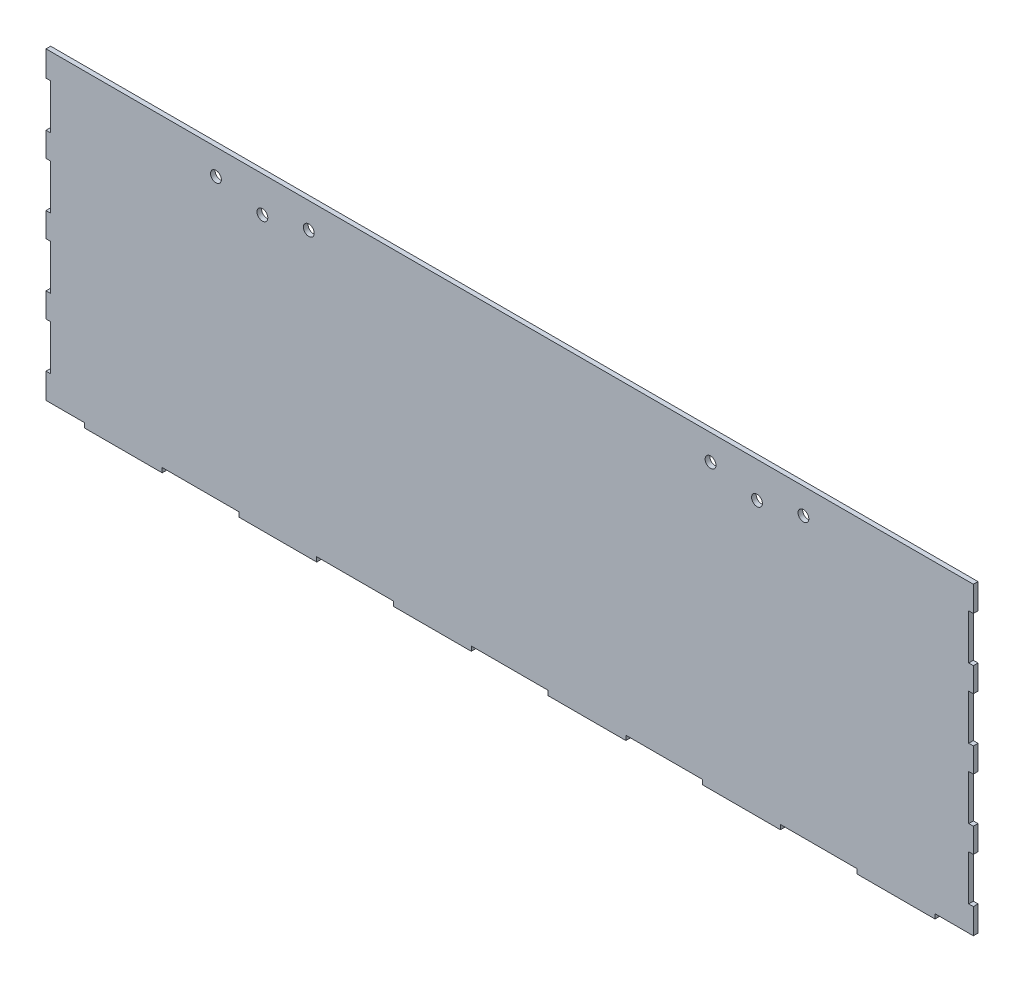
SolidWorks part; units mm, degrees
ref_plane "Alzado" through (0, 0, 0) normal (0, 0, 1) x (1, 0, 0)
ref_plane "Planta" through (0, 0, 0) normal (0, 1, 0) x (1, 0, 0)
ref_plane "Vista lateral" through (0, 0, 0) normal (1, 0, 0) x (0, 0, -1)
sketch "Croquis1" plane through (0, 0, 0) normal (0, 0, 1) x (1, 0, 0)
  line L1 (-300, 100) -> (300, 100)
  line L2 (-300, 100) -> (-300, -100)
  line L3 (-300, -100) -> (300, -100)
  line L4 (300, 100) -> (300, -100)
  line L5 (-300, 100) -> (300, -100) construction
  line L6 (-300, -100) -> (300, 100) construction
  point P0 (0, 0)
  dimension "D1" = 600
  dimension "D2" = 200
extrude "Saliente-Extruir1" add sketch "Croquis1" along normal blind 3
sketch "Croquis2" plane through (0, 0, 0) normal (0, 0, -1) x (-1, 0, 0)
  line L4 (-300, 100) -> (-300, -100)
  line L5 (-300, -100) -> (300, -100)
  line L6 (300, -100) -> (300, 100)
  line L7 (300, 100) -> (-300, 100)
  line L9 (-300, -100) -> (300, -100)
  line L11 (300, 100) -> (-300, 100)
  line L68 (224.85, -100) -> (275.15, -100)
  line L69 (275.15, -100) -> (275.15, -97)
  line L70 (275.15, -97) -> (300, -97)
  line L71 (300, -97) -> (300, -81)
  line L72 (300, -81) -> (297, -81)
  line L73 (297, -81) -> (297, -51)
  line L74 (297, -51) -> (300, -51)
  line L75 (300, -51) -> (300, -36)
  line L76 (300, -36) -> (297, -36)
  line L77 (297, -36) -> (297, -6)
  line L78 (297, -6) -> (300, -6)
  line L79 (300, -6) -> (300, 9)
  line L80 (300, 9) -> (297, 9)
  line L81 (297, 9) -> (297, 39)
  line L82 (297, 39) -> (300, 39)
  line L83 (300, 39) -> (300, 54)
  line L84 (300, 54) -> (297, 54)
  line L85 (297, 54) -> (297, 84)
  line L86 (297, 84) -> (300, 84)
  line L87 (300, 84) -> (300, 100)
  line L88 (300, 100) -> (-300, 100)
  line L89 (-300, 100) -> (-300, 84)
  line L90 (-300, 84) -> (-297, 84)
  line L91 (-297, 84) -> (-297, 54)
  line L92 (-297, 54) -> (-300, 54)
  line L93 (-300, 54) -> (-300, 39)
  line L94 (-300, 39) -> (-297, 39)
  line L95 (-297, 39) -> (-297, 9)
  line L96 (-297, 9) -> (-300, 9)
  line L97 (-300, 9) -> (-300, -6)
  line L98 (-300, -6) -> (-297, -6)
  line L99 (-297, -6) -> (-297, -36)
  line L100 (-297, -36) -> (-300, -36)
  line L101 (-300, -36) -> (-300, -51)
  line L102 (-300, -51) -> (-297, -51)
  line L103 (-297, -51) -> (-297, -81)
  line L104 (-297, -81) -> (-300, -81)
  line L105 (-300, -81) -> (-300, -97)
  line L106 (-300, -97) -> (-275.15, -97)
  line L107 (-275.15, -97) -> (-275.15, -100)
  line L108 (-275.15, -100) -> (-224.85, -100)
  line L109 (-224.85, -100) -> (-224.85, -97)
  line L110 (-224.85, -97) -> (-175.15, -97)
  line L111 (-175.15, -97) -> (-175.15, -100)
  line L112 (-175.15, -100) -> (-124.85, -100)
  line L113 (-124.85, -100) -> (-124.85, -97)
  line L114 (-124.85, -97) -> (-75.15, -97)
  line L115 (-75.15, -97) -> (-75.15, -100)
  line L116 (-75.15, -100) -> (-24.85, -100)
  line L117 (-24.85, -100) -> (-24.85, -97)
  line L118 (-24.85, -97) -> (24.85, -97)
  line L119 (24.85, -97) -> (24.85, -100)
  line L120 (24.85, -100) -> (75.15, -100)
  line L121 (75.15, -100) -> (75.15, -97)
  line L122 (75.15, -97) -> (124.85, -97)
  line L123 (124.85, -97) -> (124.85, -100)
  line L124 (124.85, -100) -> (175.15, -100)
  line L125 (175.15, -100) -> (175.15, -97)
  line L126 (175.15, -97) -> (224.85, -97)
  line L127 (224.85, -97) -> (224.85, -100)
  line L128 (224.85, -100) -> (275.15, -100)
  line L129 (275.15, -100) -> (275.15, -97)
  line L130 (275.15, -97) -> (300, -97)
  line L148 (300, 100) -> (-300, 100)
  line L166 (-300, -97) -> (-275.15, -97)
  line L167 (-275.15, -97) -> (-275.15, -100)
  line L168 (-275.15, -100) -> (-224.85, -100)
  line L169 (-224.85, -100) -> (-224.85, -97)
  line L170 (-224.85, -97) -> (-175.15, -97)
  line L171 (-175.15, -97) -> (-175.15, -100)
  line L172 (-175.15, -100) -> (-124.85, -100)
  line L173 (-124.85, -100) -> (-124.85, -97)
  line L174 (-124.85, -97) -> (-75.15, -97)
  line L175 (-75.15, -97) -> (-75.15, -100)
  line L176 (-75.15, -100) -> (-24.85, -100)
  line L177 (-24.85, -100) -> (-24.85, -97)
  line L178 (-24.85, -97) -> (24.85, -97)
  line L179 (24.85, -97) -> (24.85, -100)
  line L180 (24.85, -100) -> (75.15, -100)
  line L181 (75.15, -100) -> (75.15, -97)
  line L182 (75.15, -97) -> (124.85, -97)
  line L183 (124.85, -97) -> (124.85, -100)
  line L184 (124.85, -100) -> (175.15, -100)
  line L185 (175.15, -100) -> (175.15, -97)
  line L186 (175.15, -97) -> (224.85, -97)
  line L187 (224.85, -97) -> (224.85, -100)
  line L548 (-300, -97) -> (-300, 100)
  line L549 (300, -100) -> (300, 100)
  line L731 (-297, -51.4) -> (-300, -51.4)
  line L732 (-297, -51.4) -> (-297, -80.6)
  line L733 (-297, -80.6) -> (-300, -80.6)
  line L734 (-300, -51.4) -> (-300, -80.6)
  line L1814 (-297, -6.4) -> (-297, -35.6)
  line L1815 (-297, -6.4) -> (-300, -6.4)
  line L1816 (-300, -6.4) -> (-300, -35.6)
  line L1817 (-297, -35.6) -> (-300, -35.6)
  line L1818 (-297, 38.6) -> (-297, 9.4)
  line L1819 (-297, 38.6) -> (-300, 38.6)
  line L1820 (-300, 38.6) -> (-300, 9.4)
  line L1821 (-297, 9.4) -> (-300, 9.4)
  line L1822 (-297, 83.6) -> (-297, 54.4)
  line L1823 (-297, 83.6) -> (-300, 83.6)
  line L1824 (-300, 83.6) -> (-300, 54.4)
  line L1825 (-297, 54.4) -> (-300, 54.4)
  line L1826 (0, 0) -> (0, 54.4) construction
  line L1827 (297, -80.6) -> (300, -80.6)
  line L1828 (300, -51.4) -> (300, -80.6)
  line L1829 (297, -51.4) -> (300, -51.4)
  line L1830 (297, -51.4) -> (297, -80.6)
  line L1831 (297, -6.4) -> (300, -6.4)
  line L1832 (300, -6.4) -> (300, -35.6)
  line L1833 (297, -35.6) -> (300, -35.6)
  line L1834 (297, -6.4) -> (297, -35.6)
  line L1835 (297, 38.6) -> (300, 38.6)
  line L1836 (300, 38.6) -> (300, 9.4)
  line L1837 (297, 9.4) -> (300, 9.4)
  line L1838 (297, 38.6) -> (297, 9.4)
  line L1839 (297, 83.6) -> (300, 83.6)
  line L1840 (300, 83.6) -> (300, 54.4)
  line L1841 (297, 54.4) -> (300, 54.4)
  line L1842 (297, 83.6) -> (297, 54.4)
  dimension "D3" = 0
  dimension "D4" = 29.2
  dimension "D5" = 3
  dimension "D6" = 19.4
  dimension "D8" = 45
  dimension "D1" = 0
  dimension "D2" = 0
  dimension "D7" = 4
extrude "Cortar-Extruir1" cut sketch "Croquis2" against normal through all
sketch "Croquis3" plane through (0, 0, 3) normal (0, 0, 1) x (1, 0, 0)
  arc A2 (-163.5, 77) -> (-156.5, 77) centre (-160, 77) ccw
  arc A3 (-156.5, 77) -> (-163.5, 77) centre (-160, 77) ccw
  arc A4 (-163.5, 77) -> (-156.5, 77) centre (-160, 77) ccw
  arc A5 (-156.5, 77) -> (-163.5, 77) centre (-160, 77) ccw
  arc A6 (-133.45, 83.4) -> (-126.45, 83.4) centre (-129.95, 83.4) ccw
  arc A7 (-126.45, 83.4) -> (-133.45, 83.4) centre (-129.95, 83.4) ccw
  arc A8 (-133.45, 83.4) -> (-126.45, 83.4) centre (-129.95, 83.4) ccw
  arc A9 (-126.45, 83.4) -> (-133.45, 83.4) centre (-129.95, 83.4) ccw
  arc A10 (126.45, 83.4) -> (133.45, 83.4) centre (129.95, 83.4) ccw
  arc A11 (133.45, 83.4) -> (126.45, 83.4) centre (129.95, 83.4) ccw
  arc A12 (126.45, 83.4) -> (133.45, 83.4) centre (129.95, 83.4) ccw
  arc A13 (133.45, 83.4) -> (126.45, 83.4) centre (129.95, 83.4) ccw
  arc A14 (156.5, 77) -> (163.5, 77) centre (160, 77) ccw
  arc A15 (163.5, 77) -> (156.5, 77) centre (160, 77) ccw
  arc A16 (156.5, 77) -> (163.5, 77) centre (160, 77) ccw
  arc A17 (163.5, 77) -> (156.5, 77) centre (160, 77) ccw
  arc A18 (186.55, 83.4) -> (193.55, 83.4) centre (190.05, 83.4) ccw
  arc A19 (193.55, 83.4) -> (186.55, 83.4) centre (190.05, 83.4) ccw
  arc A20 (186.55, 83.4) -> (193.55, 83.4) centre (190.05, 83.4) ccw
  arc A21 (193.55, 83.4) -> (186.55, 83.4) centre (190.05, 83.4) ccw
  arc A22 (-193.55, 83.4) -> (-186.55, 83.4) centre (-190.05, 83.4) ccw
  arc A23 (-186.55, 83.4) -> (-193.55, 83.4) centre (-190.05, 83.4) ccw
  arc A24 (-193.55, 83.4) -> (-186.55, 83.4) centre (-190.05, 83.4) ccw
  arc A25 (-186.55, 83.4) -> (-193.55, 83.4) centre (-190.05, 83.4) ccw
  dimension "D1" = 0
  dimension "D2" = 0
  dimension "D3" = 0
  dimension "D4" = 0
  dimension "D5" = 0
  dimension "D6" = 0
extrude "Cortar-Extruir2" cut sketch "Croquis3" against normal through all
